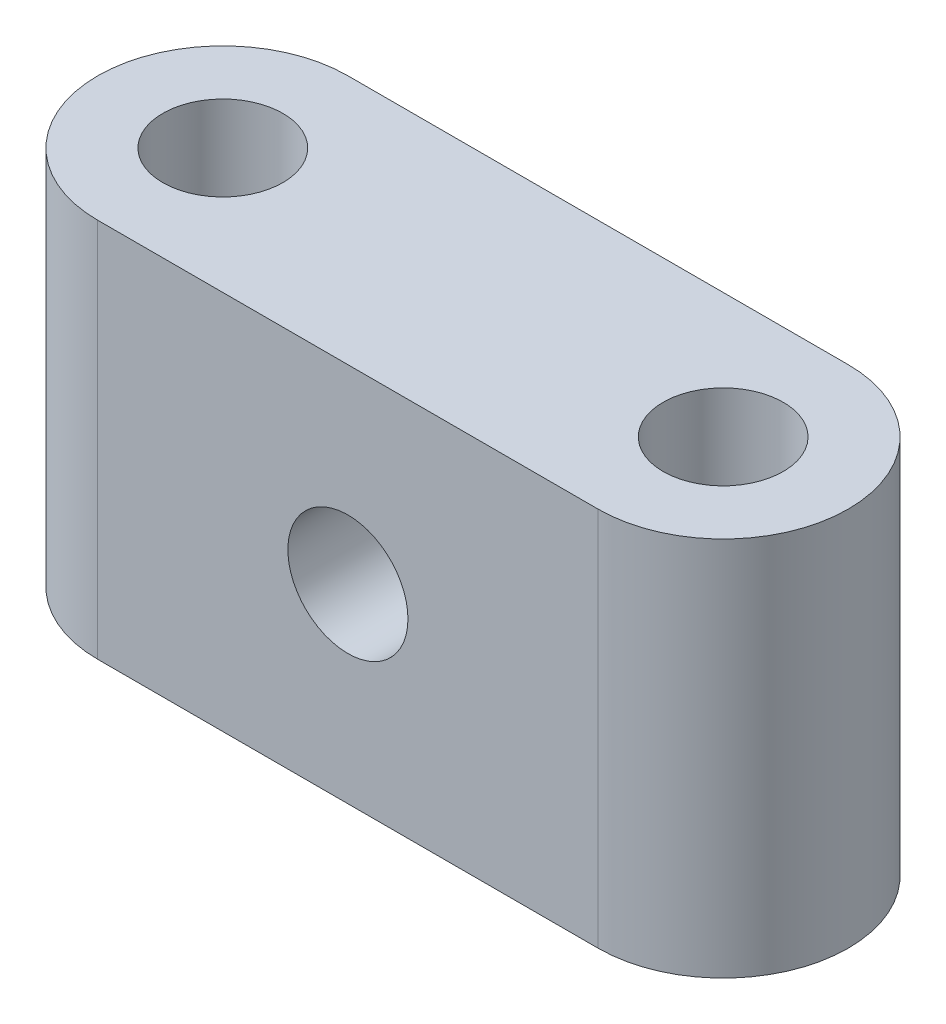
SolidWorks part; units mm, degrees
ref_plane "Front Plane" through (0, 0, 0) normal (0, 0, 1) x (1, 0, 0)
ref_plane "Top Plane" through (0, 0, 0) normal (0, 1, 0) x (1, 0, 0)
ref_plane "Right Plane" through (0, 0, 0) normal (1, 0, 0) x (0, 0, -1)
sketch "Sketch1" plane through (0, 0, 0) normal (0, 1, 0) x (1, 0, 0)
  line L0 (0, 0) -> (50, 0) construction
  line L1 (0, 12.5) -> (50, 12.5)
  line L2 (0, -12.5) -> (50, -12.5)
  arc A0 (0, 12.5) -> (0, -12.5) centre (0, 0) ccw
  arc A1 (50, -12.5) -> (50, 12.5) centre (50, 0) ccw
  circle A2 centre (0, 0) radius 6
  circle A3 centre (50, 0) radius 6
  point P3 (25, 0)
  dimension "D2" = 12.5
  dimension "D3" = 12
  dimension "D1" = 50
sketch "Sketch2" plane through (0, 0, 0) normal (0, 1, 0) x (1, 0, 0)
extrude "Boss-Extrude1" add sketch "Sketch1" along normal blind 38
sketch "Sketch3" plane through (0, 0, 12.5) normal (0, 0, 1) x (1, 0, 0)
  line L0 (25, 0) -> (25, 38) construction
  line L1 (0, 0) -> (50, 0) construction
  line L2 (0, 38) -> (50, 38) construction
  circle A0 centre (25, 19) radius 6
  dimension "D1" = 12
extrude "Cut-Extrude1" cut sketch "Sketch3" against normal blind 38
